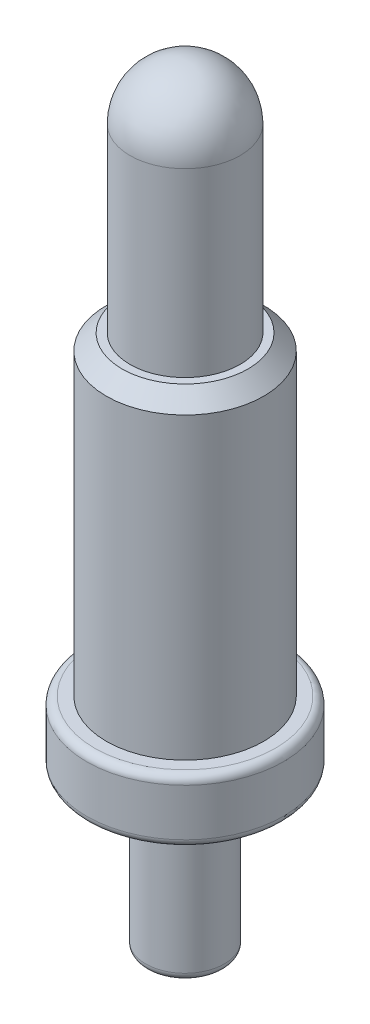
SolidWorks part; units mm, degrees
ref_plane "前视基准面" through (0, 0, 0) normal (0, 0, 1) x (1, 0, 0)
ref_plane "上视基准面" through (0, 0, 0) normal (0, 1, 0) x (1, 0, 0)
ref_plane "右视基准面" through (0, 0, 0) normal (1, 0, 0) x (0, 0, -1)
sketch "草图1" plane through (0, 0, 0) normal (0, 1, 0) x (1, 0, 0)
  circle A0 centre (0, 0) radius 0.5
  dimension "D1" = 1
extrude "凸台-拉伸1" add sketch "草图1" against normal blind 2
sketch "草图2" plane through (0, 0, 0) normal (0, 1, 0) x (1, 0, 0)
  circle A0 centre (0, 0) radius 1.25
  dimension "D1" = 2.5
extrude "凸台-拉伸2" add sketch "草图2" along normal blind 0.8
sketch "草图3" plane through (0, 0.8, 0) normal (0, 1, 0) x (1, 0, 0)
  circle A0 centre (0, 0) radius 1
  dimension "D1" = 2
extrude "凸台-拉伸3" add sketch "草图3" along normal blind 4
sketch "草图4" plane through (0, 4.8, 0) normal (0, 1, 0) x (1, 0, 0)
  circle A0 centre (0, 0) radius 0.7
  dimension "D1" = 1.4
extrude "凸台-拉伸4" add sketch "草图4" along normal blind 3
fillet "圆角1" radius 0.7 1 edges at (0, 7.8, 0.7)
chamfer "倒角1" distance 0.2 angle 45 1 edges at (0, 4.8, 1)
fillet "圆角2" radius 0.1 3 edges at (0, -2, 0.5) (0, 0, 1.25) (0, 0.8, 1.25)
